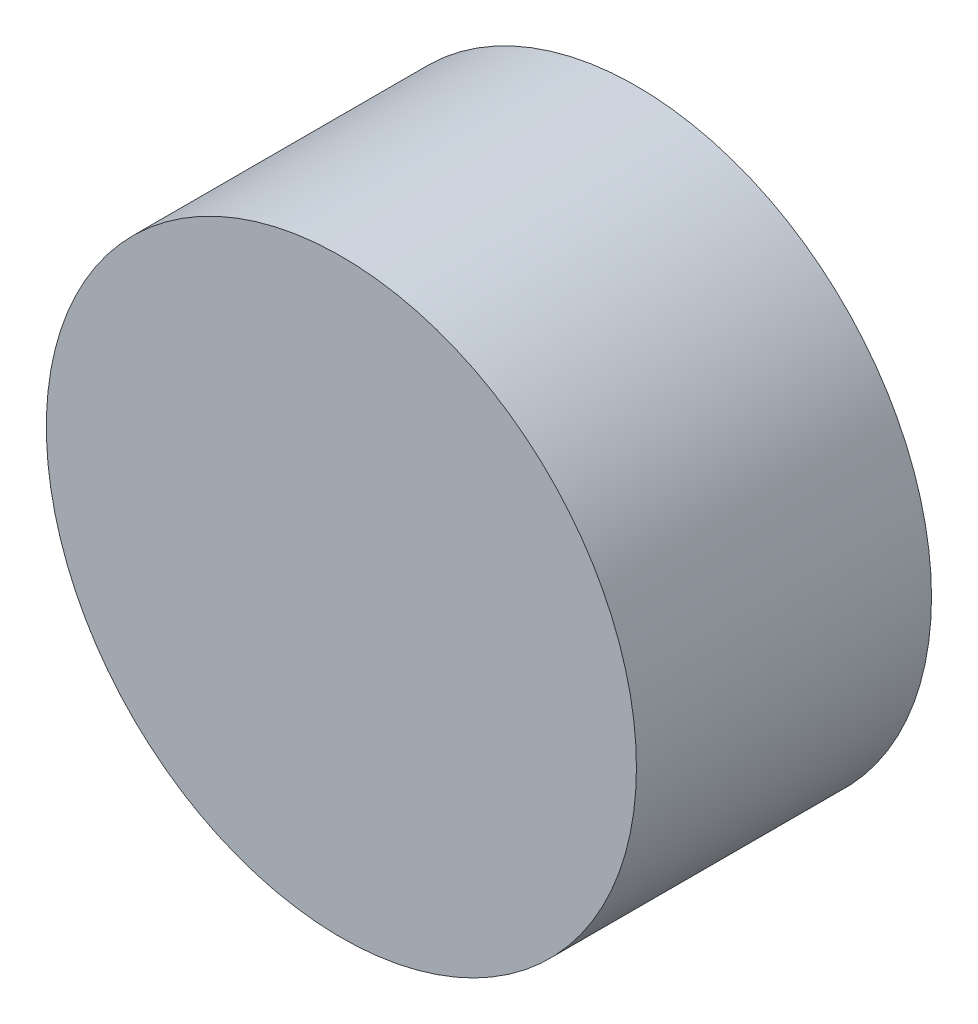
SolidWorks part; units mm, degrees
ref_plane "Front Plane" through (0, 0, 0) normal (0, 0, 1) x (1, 0, 0)
ref_plane "Top Plane" through (0, 0, 0) normal (0, 1, 0) x (1, 0, 0)
ref_plane "Right Plane" through (0, 0, 0) normal (1, 0, 0) x (0, 0, -1)
sketch "Sketch1" plane through (0, 0, 0) normal (0, 0, 1) x (1, 0, 0)
  circle A0 centre (0, 0) radius 203.2
  dimension "D1" = 406.4
extrude "Boss-Extrude1" add sketch "Sketch1" along normal mid plane 203.2
